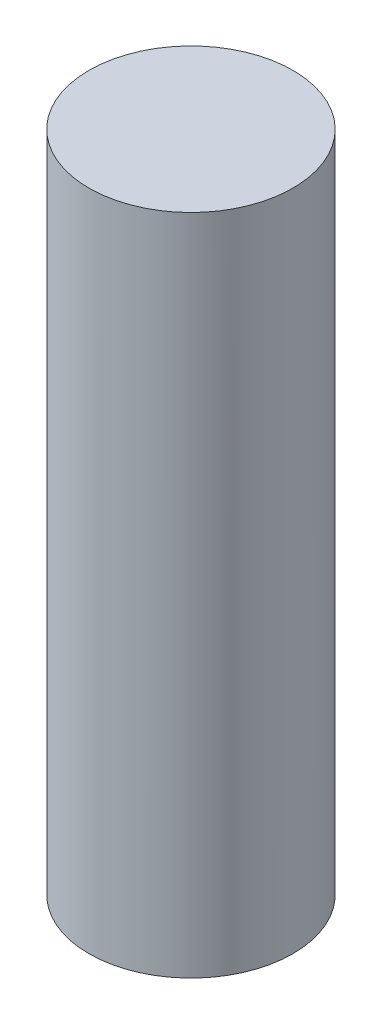
SolidWorks part; units mm, degrees
material "7075-T6 (SN)"
ref_plane "Front Plane" through (0, 0, 0) normal (0, 0, 1) x (1, 0, 0)
ref_plane "Top Plane" through (0, 0, 0) normal (0, 1, 0) x (1, 0, 0)
ref_plane "Right Plane" through (0, 0, 0) normal (1, 0, 0) x (0, 0, -1)
sketch "Sketch1" plane through (0, 0, 0) normal (0, 0, 1) x (1, 0, 0)
  line L0 (0, 0) -> (-3, 0)
  line L1 (-3, 0) -> (-3, 1)
  line L2 (-3, 1) -> (-2, 1)
  line L3 (-2, 1) -> (-2, 13)
  line L4 (-2, 13) -> (0, 13)
  line L5 (0, 13) -> (0, 0)
  dimension "D1" = 2
  dimension "D2" = 3
  dimension "D3" = 1
  dimension "D4" = 13
revolve "Revolve1" add sketch "Sketch1" angle 360 about L5
sketch "Sketch2" plane through (0, 1, 0) normal (0, 1, 0) x (1, 0, 0)
  circle A0 centre (0, 0) radius 2 construction
  circle A1 centre (0, 0) radius 2
  circle A2 centre (0, 0) radius 3 construction
  circle A3 centre (0, 0) radius 3
extrude "Cut-Extrude1" cut sketch "Sketch2" against normal up to next
